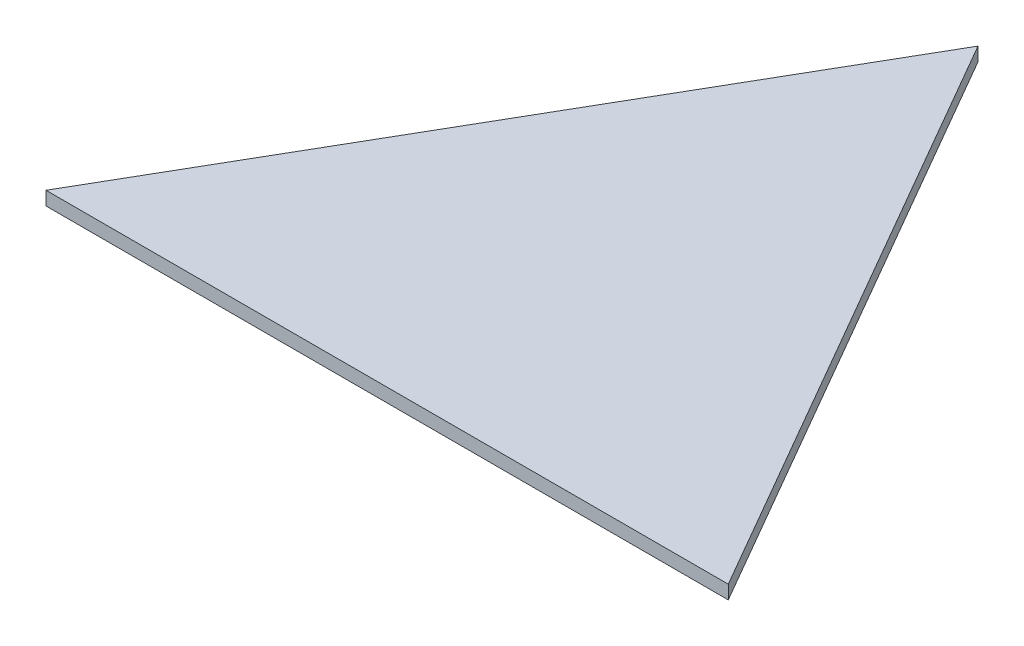
SolidWorks part; units mm, degrees
ref_plane "Front Plane" through (0, 0, 0) normal (0, 0, 1) x (1, 0, 0)
ref_plane "Top Plane" through (0, 0, 0) normal (0, 1, 0) x (1, 0, 0)
ref_plane "Right Plane" through (0, 0, 0) normal (1, 0, 0) x (0, 0, -1)
sketch "Sketch2" plane through (0, 0, 0) normal (0, 1, 0) x (1, 0, 0)
  line L4 (-75, -54.9038) -> (75, -54.9038)
  line L9 (-75, -54.9038) -> (0, 75)
  line L15 (75, -54.9038) -> (0, 75)
  dimension "D1" = 150
  dimension "D2" = 150
  dimension "D3" = 150
  dimension "D4" = 75
extrude "Boss-Extrude1" add sketch "Sketch2" along normal blind 3 contours L9 L15 L4
